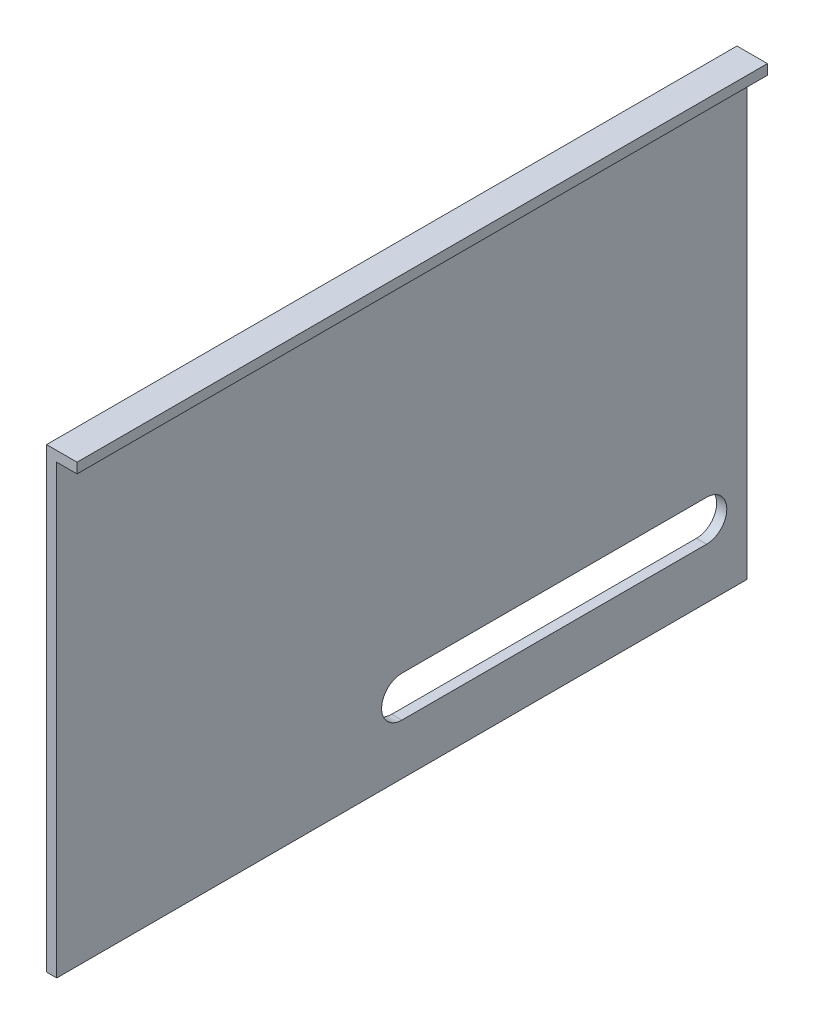
SolidWorks part; units mm, degrees
material "Acrylic (Medium-high impact)"
ref_plane "Front" through (0, 0, 0) normal (0, 0, 1) x (1, 0, 0)
ref_plane "Top" through (0, 0, 0) normal (0, 1, 0) x (1, 0, 0)
ref_plane "Right" through (0, 0, 0) normal (1, 0, 0) x (0, 0, -1)
sketch "Sketch1" plane through (0, 0, 0) normal (1, 0, 0) x (0, 0, -1)
  line L1 (-215.9, 142.875) -> (215.9, 142.875)
  line L2 (-215.9, 142.875) -> (-215.9, -142.875)
  line L3 (-215.9, -142.875) -> (215.9, -142.875)
  line L4 (215.9, 142.875) -> (215.9, -142.875)
  point P4 (-215.9, 0)
  point P6 (0, 142.875)
  dimension "D1" = 285.75
  dimension "D2" = 431.8
extrude "Boss-Extrude1" add sketch "Sketch1" along normal blind 6.35
sketch "Sketch2" plane through (6.35, 0, 0) normal (1, 0, 0) x (0, 0, -1)
  line L0 (215.9, -142.875) -> (215.9, 142.875) construction
  line L1 (-215.9, 142.875) -> (215.9, 142.875)
  line L2 (-215.9, 142.875) -> (-215.9, 136.525)
  line L3 (-215.9, 136.525) -> (215.9, 136.525)
  line L4 (215.9, 142.875) -> (215.9, 136.525)
  dimension "D1" = 6.35
extrude "Boss-Extrude2" add sketch "Sketch2" along normal blind 12.7
sketch "Sketch3" plane through (0, 0, 0) normal (-1, 0, 0) x (0, 0, 1)
  line L0 (-190.5, -85.725) -> (0, -85.725)
  line L1 (0, -111.125) -> (-190.5, -111.125)
  line L2 (38.1, 142.875) -> (38.1, -142.875) construction
  line L3 (-215.9, 142.875) -> (215.9, 142.875) construction
  line L4 (215.9, -142.875) -> (-215.9, -142.875) construction
  line L5 (215.9, 142.875) -> (215.9, -142.875) construction
  arc A0 (0, -85.725) -> (0, -111.125) centre (0, -98.425) cw
  arc A1 (-190.5, -111.125) -> (-190.5, -85.725) centre (-190.5, -98.425) cw
  dimension "D1" = 25.4
  dimension "D3" = 190.5
  dimension "D2" = 38.1
  dimension "D4" = 177.8
  dimension "D5" = 44.45
extrude "Cut-Extrude1" cut sketch "Sketch3" against normal through all
